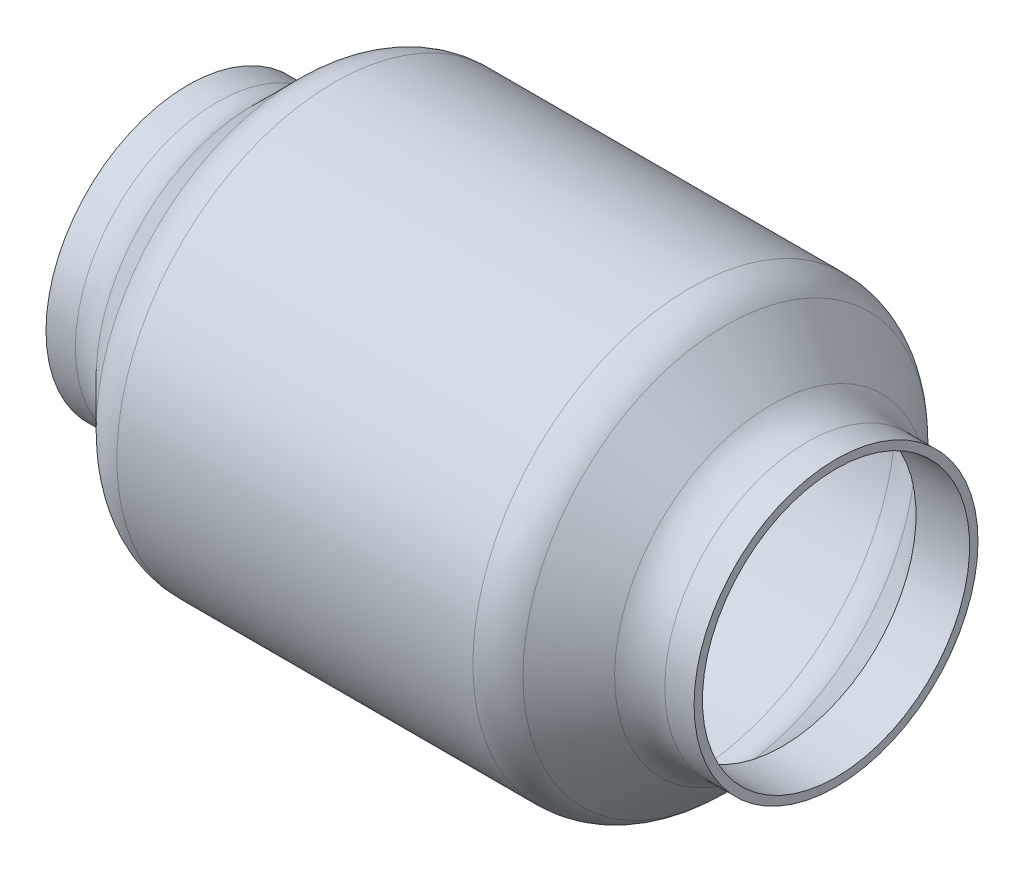
SolidWorks part; units mm, degrees
material "PVC Rigid"
ref_plane "Front Plane" through (0, 0, 0) normal (0, 0, 1) x (1, 0, 0)
ref_plane "Top Plane" through (0, 0, 0) normal (0, 1, 0) x (1, 0, 0)
ref_plane "Right Plane" through (0, 0, 0) normal (1, 0, 0) x (0, 0, -1)
sketch "Sketch1" plane through (0, 0, 0) normal (0, 0, 1) x (1, 0, 0)
  line L0 (-123.19, 0) -> (123.19, 0) construction
  line L1 (-123.19, 53.975) -> (-123.19, 50.8)
  line L2 (-123.19, 50.8) -> (-102.8249, 50.8)
  line L3 (-102.8249, 50.8) -> (-79.8295, 73.7954)
  line L4 (-66.3591, 79.375) -> (66.3591, 79.375)
  line L5 (79.8295, 73.7954) -> (102.8249, 50.8)
  line L6 (102.8249, 50.8) -> (123.19, 50.8)
  line L7 (123.19, 50.8) -> (123.19, 53.975)
  line L8 (123.19, 53.975) -> (112.0308, 53.975)
  line L9 (98.5604, 59.5546) -> (81.1446, 76.9704)
  line L10 (67.6742, 82.55) -> (-67.6742, 82.55)
  line L11 (-81.1446, 76.9704) -> (-98.5604, 59.5546)
  line L12 (-112.0308, 53.975) -> (-123.19, 53.975)
  arc A0 (-67.6742, 82.55) -> (-81.1446, 76.9704) centre (-67.6742, 63.5) ccw
  arc A1 (-66.3591, 79.375) -> (-79.8295, 73.7954) centre (-66.3591, 60.325) ccw
  arc A2 (81.1446, 76.9704) -> (67.6742, 82.55) centre (67.6742, 63.5) ccw
  arc A3 (66.3591, 79.375) -> (79.8295, 73.7954) centre (66.3591, 60.325) cw
  arc A4 (112.0308, 53.975) -> (98.5604, 59.5546) centre (112.0308, 73.025) cw
  arc A5 (-98.5604, 59.5546) -> (-112.0308, 53.975) centre (-112.0308, 73.025) cw
  point P3 (0, 0)
  point P4 (123.19, 52.3875)
  point P15 (-111.9487, 47.625)
  point P18 (110.6326, 47.625)
  point P19 (87.447, 79.375)
  point P20 (-81.9524, 82.55)
  point P21 (-118.4697, 50.8)
  point P22 (86.2877, 82.55)
  point P23 (-58.0423, 79.375)
  point P24 (-72.2435, 79.375)
  point P25 (0, 79.375)
  point P26 (-123.19, 0)
  point P27 (123.19, 0)
  point P38 (104.14, 53.975)
  point P41 (-104.14, 53.975)
  dimension "D12" = 19.05
  dimension "D1" = 246.38
  dimension "D2" = 82.55
  dimension "D3" = 50.8
  dimension "D4" = 3.175
  dimension "D5" = 3.175
  dimension "D6" = 3.175
  dimension "D7" = 3.175
  dimension "D8" = 135
  dimension "D9" = 135
  dimension "D10" = 19.05
  dimension "D11" = 19.05
revolve "Revolve1" add sketch "Sketch1" angle 360 about L0
